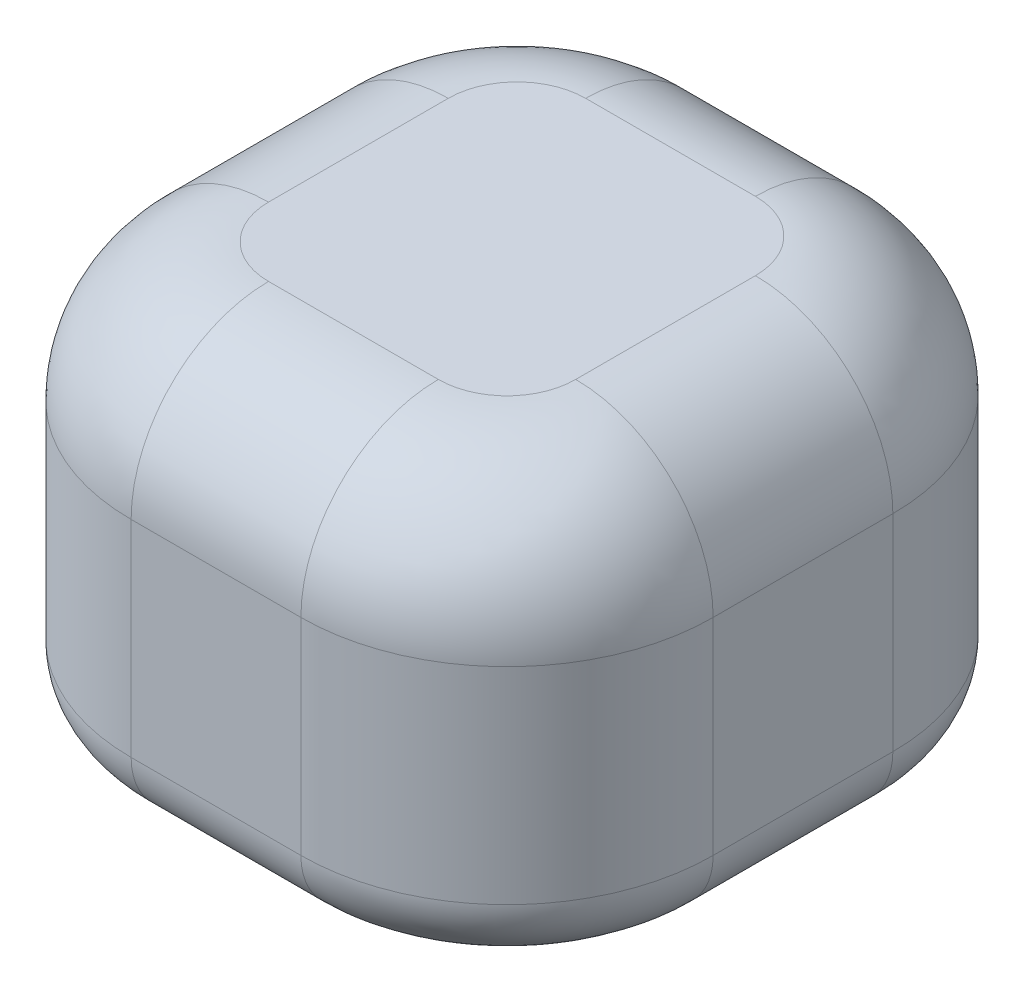
SolidWorks part; units mm, degrees
ref_plane "Front Plane" through (0, 0, 0) normal (0, 0, 1) x (1, 0, 0)
ref_plane "Top Plane" through (0, 0, 0) normal (0, 1, 0) x (1, 0, 0)
ref_plane "Right Plane" through (0, 0, 0) normal (1, 0, 0) x (0, 0, -1)
sketch "Sketch1" plane through (0, 0, 0) normal (0, 1, 0) x (1, 0, 0)
  line L0 (-96.2108, -81.7523) -> (106.8591, 64.0647) construction
  line L1 (-42.3542, -43.0799) -> (42.3542, -43.0799)
  line L2 (-42.3542, -43.0799) -> (-42.3542, 43.0799)
  line L3 (-42.3542, 43.0799) -> (42.3542, 43.0799)
  line L4 (42.3542, -43.0799) -> (42.3542, 43.0799)
  line L5 (-42.3542, -43.0799) -> (42.3542, 43.0799) construction
  line L6 (-42.3542, 43.0799) -> (42.3542, -43.0799) construction
  point P0 (0, 0)
extrude "Boss-Extrude1" add sketch "Sketch1" along normal blind 30 and the other way blind 30
fillet "Fillet1" radius 30 4 edges at (42.3542, 0, 43.0799) (42.3542, 0, -43.0799) (-42.3542, 0, 43.0799) (-42.3542, 0, -43.0799)
fillet "Fillet2" radius 20 8 edges at (-33.5674, 30, 34.2931) (-42.3542, 30, 0) (-33.5674, 30, -34.2931) (0, 30, -43.0799) (33.5674, 30, -34.2931) (42.3542, 30, 0) (33.5674, 30, 34.2931) (0, 30, 43.0799)
fillet "Fillet3" radius 10 8 edges at (33.5674, -30, -34.2931) (0, -30, -43.0799) (-33.5674, -30, -34.2931) (-42.3542, -30, 0) (-33.5674, -30, 34.2931) (0, -30, 43.0799) (33.5674, -30, 34.2931) (42.3542, -30, 0)
